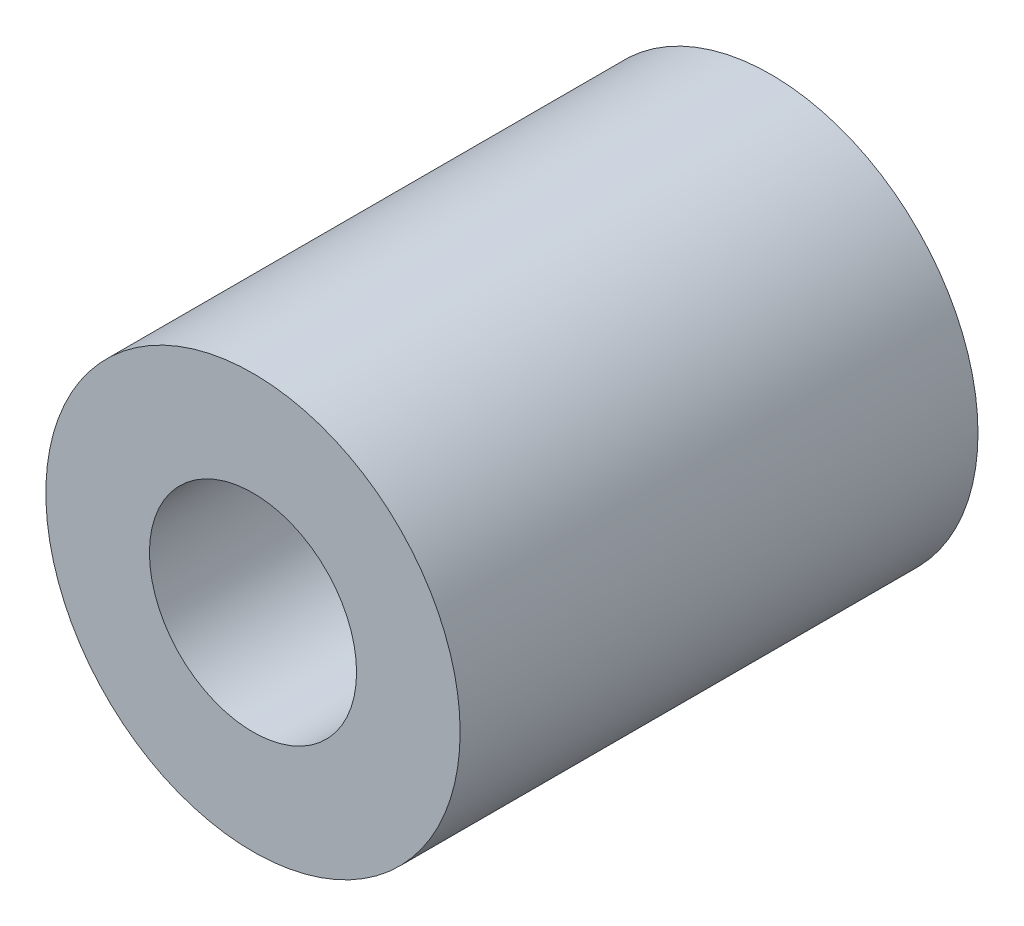
SolidWorks part; units mm, degrees
material "Custom Plastic"
ref_plane "X-Y Datum" through (0, 0, 0) normal (0, 0, 1) x (1, 0, 0)
ref_plane "X-Z Datum" through (0, 0, 0) normal (0, 1, 0) x (1, 0, 0)
ref_plane "Y-Z Datum" through (0, 0, 0) normal (1, 0, 0) x (0, 0, -1)
sketch "Base Sketch" plane through (0, 0, 0) normal (0, 0, 1) x (1, 0, 0)
  circle A0 centre (0, 0) radius 2
  circle A1 centre (0, 0) radius 1
  dimension "D1" = 4
  dimension "D2" = 2
extrude "Extrude Pin" add sketch "Base Sketch" along normal blind 5
